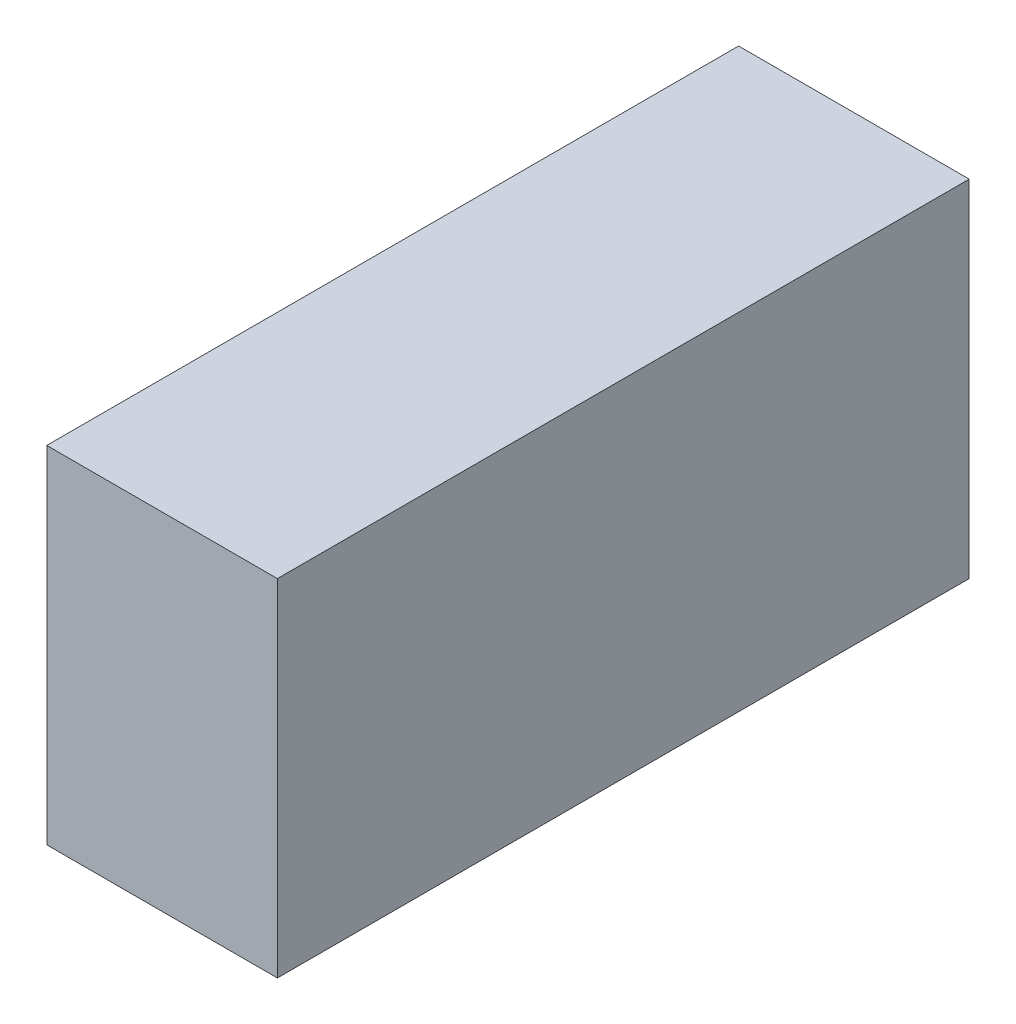
SolidWorks part; units mm, degrees
material "6061 Alloy"
ref_plane "Front Plane" through (0, 0, 0) normal (0, 0, 1) x (1, 0, 0)
ref_plane "Top Plane" through (0, 0, 0) normal (0, 1, 0) x (1, 0, 0)
ref_plane "Right Plane" through (0, 0, 0) normal (1, 0, 0) x (0, 0, -1)
sketch "Sketch1" plane through (0, 0, 0) normal (1, 0, 0) x (0, 0, -1)
  line L1 (0, 0) -> (914.4, 0)
  line L2 (0, 0) -> (0, 457.2)
  line L3 (0, 457.2) -> (914.4, 457.2)
  line L4 (914.4, 0) -> (914.4, 457.2)
  dimension "D1" = 914.4
  dimension "D2" = 457.2
extrude "Main Enclosure Model" add sketch "Sketch1" along normal blind 304.8
